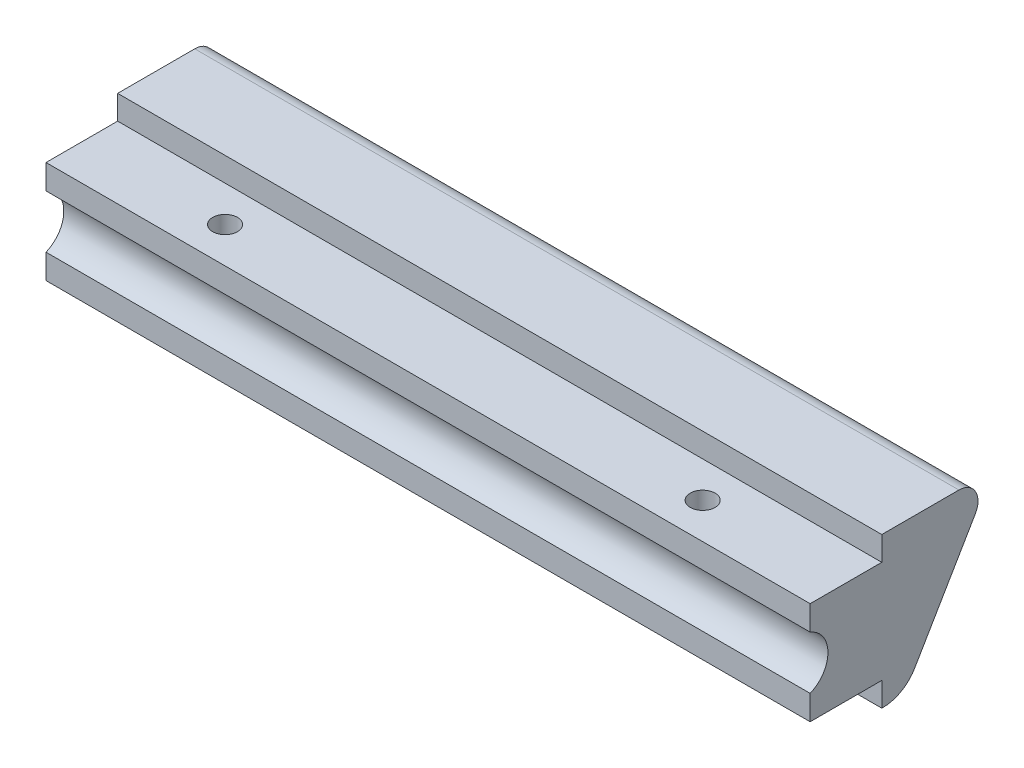
SolidWorks part; units mm, degrees
ref_plane "Front Plane" through (0, 0, 0) normal (0, 0, 1) x (1, 0, 0)
ref_plane "Top Plane" through (0, 0, 0) normal (0, 1, 0) x (1, 0, 0)
ref_plane "Right Plane" through (0, 0, 0) normal (1, 0, 0) x (0, 0, -1)
sketch "Sketch1" plane through (0, 0, 0) normal (1, 0, 0) x (0, 0, -1)
  line L0 (0, 16.7996) -> (0, 3.2004)
  line L1 (0, 20) -> (9.672, 20) construction
  line L2 (0, 20) -> (0, 0) construction
  line L3 (0, 0) -> (9.672, 0) construction
  line L4 (9.672, 20) -> (9.672, 0) construction
  line L5 (0, 20) -> (9.672, 20) construction
  line L6 (0, 20) -> (0, 16.7996) construction
  line L9 (0, 3.2004) -> (9.525, 3.2004)
  line L10 (0, 3.2004) -> (0, 0) construction
  line L11 (0, 0) -> (9.672, 0) construction
  line L14 (24.2156, 20) -> (13.8937, 2.417)
  line L15 (9.672, 0) -> (9.525, 0)
  line L16 (9.525, 3.2004) -> (9.525, 0)
  line L17 (24.2156, 20) -> (9.525, 20)
  line L18 (9.525, 20) -> (9.525, 16.7996)
  line L19 (9.525, 16.7996) -> (0, 16.7996)
  line L20 (39.2831, 45.6667) -> (13.8937, 2.417) construction
  arc A2 (13.8937, 2.417) -> (9.672, 0) centre (9.672, 4.8953) cw
  dimension "D4" = 9.525
  dimension "D1" = 20
  dimension "D3" = 3.2004
extrude "Boss-Extrude1" add sketch "Sketch1" along normal blind 101.6
sketch "Sketch4" plane through (0, 0, 0) normal (-1, 0, 0) x (0, 0, 1)
  line L1 (0, 13.5263) -> (0, 6.4737)
  line L2 (-18.3452, 10) -> (1.4427, 10) construction
  line L3 (0, 3.2004) -> (-9.525, 3.2004) construction
  line L4 (0, 16.7996) -> (0, 3.2004) construction
  line L5 (-13.8937, 2.417) -> (-24.2156, 20) construction
  arc A0 (0, 13.5263) -> (0, 6.4737) centre (1.4427, 10) ccw
  point P3 (0, 10)
  dimension "D1" = 3.81
  dimension "D2" = 1.4427
extrude "Cut-Extrude2" cut sketch "Sketch4" against normal up to surface (101.6 mm away) up to face at (101.6, 9.0951, -9.5781)
sketch "Sketch5" plane through (0, 16.7996, 0) normal (0, 1, 0) x (1, 0, 0)
  line L0 (50.8, 9.525) -> (50.8, 0) construction
  line L1 (19.05, 4.7625) -> (82.55, 4.7625) construction
  line L2 (101.6, 9.525) -> (0, 9.525) construction
  line L3 (101.6, 0) -> (0, 0) construction
  circle A4 centre (19.05, 4.7625) radius 1.651
  circle A5 centre (82.55, 4.7625) radius 1.651
  point P8 (50.8, 4.7625)
  dimension "D1" = 63.5
  dimension "D2" = 3.302
extrude "Cut-Extrude3" cut sketch "Sketch5" against normal up to surface (13.5992 mm away) up to face at (50.8, 3.2004, -4.7625)
fillet "Fillet1" radius 2.54 1 edges at (50.8, 20, -24.2156)
